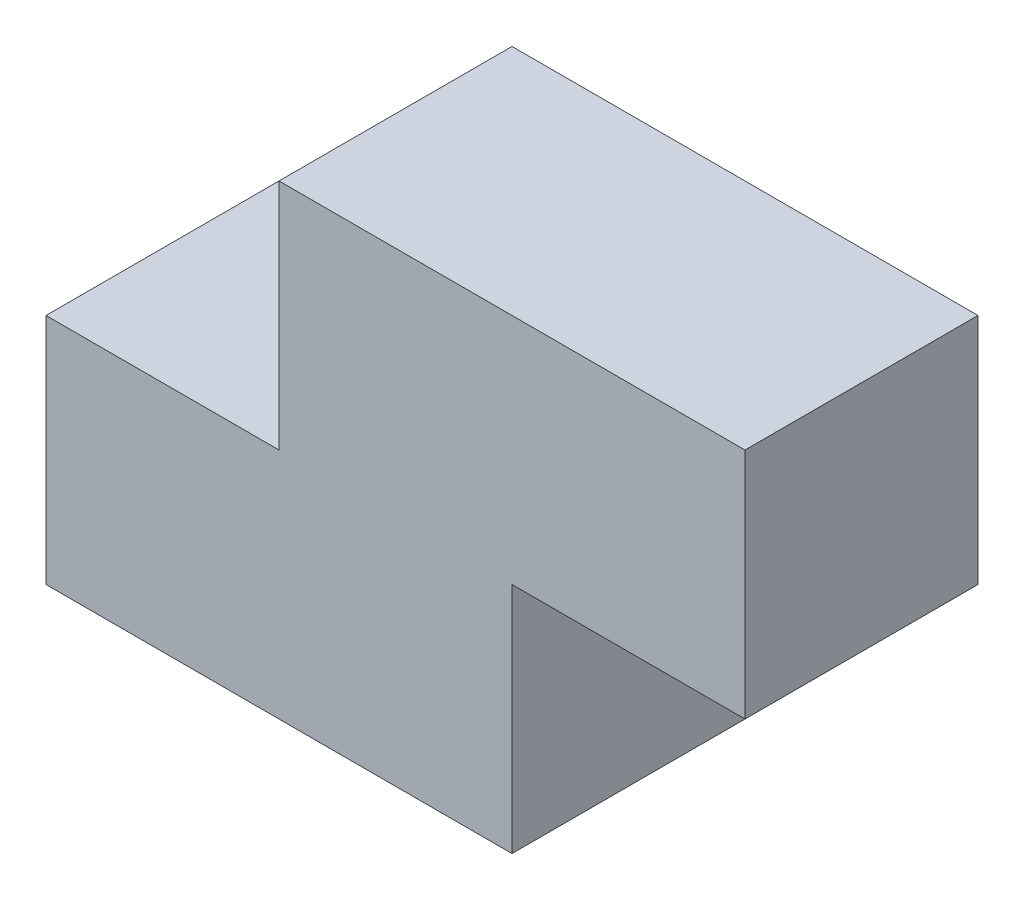
SolidWorks part; units mm, degrees
ref_plane "Plan de face" through (0, 0, 0) normal (0, 0, 1) x (1, 0, 0)
ref_plane "Plan de dessus" through (0, 0, 0) normal (0, 1, 0) x (1, 0, 0)
ref_plane "Plan de droite" through (0, 0, 0) normal (1, 0, 0) x (0, 0, -1)
sketch "Esquisse1" plane through (0, 0, 0) normal (0, 0, 1) x (1, 0, 0)
  line L0 (0, 0) -> (60, 0)
  line L1 (60, 0) -> (60, 30)
  line L2 (60, 30) -> (90, 30)
  line L3 (90, 30) -> (90, 60)
  line L4 (90, 60) -> (30, 60)
  line L5 (30, 60) -> (30, 30)
  line L6 (30, 30) -> (0, 30)
  line L7 (0, 30) -> (0, 0)
  dimension "D1" = 30
  dimension "D2" = 60
  dimension "D3" = 60
  dimension "D4" = 30
  dimension "D5" = 30
  dimension "D6" = 30
extrude "Boss.-Extru.1" add sketch "Esquisse1" along normal blind 30
